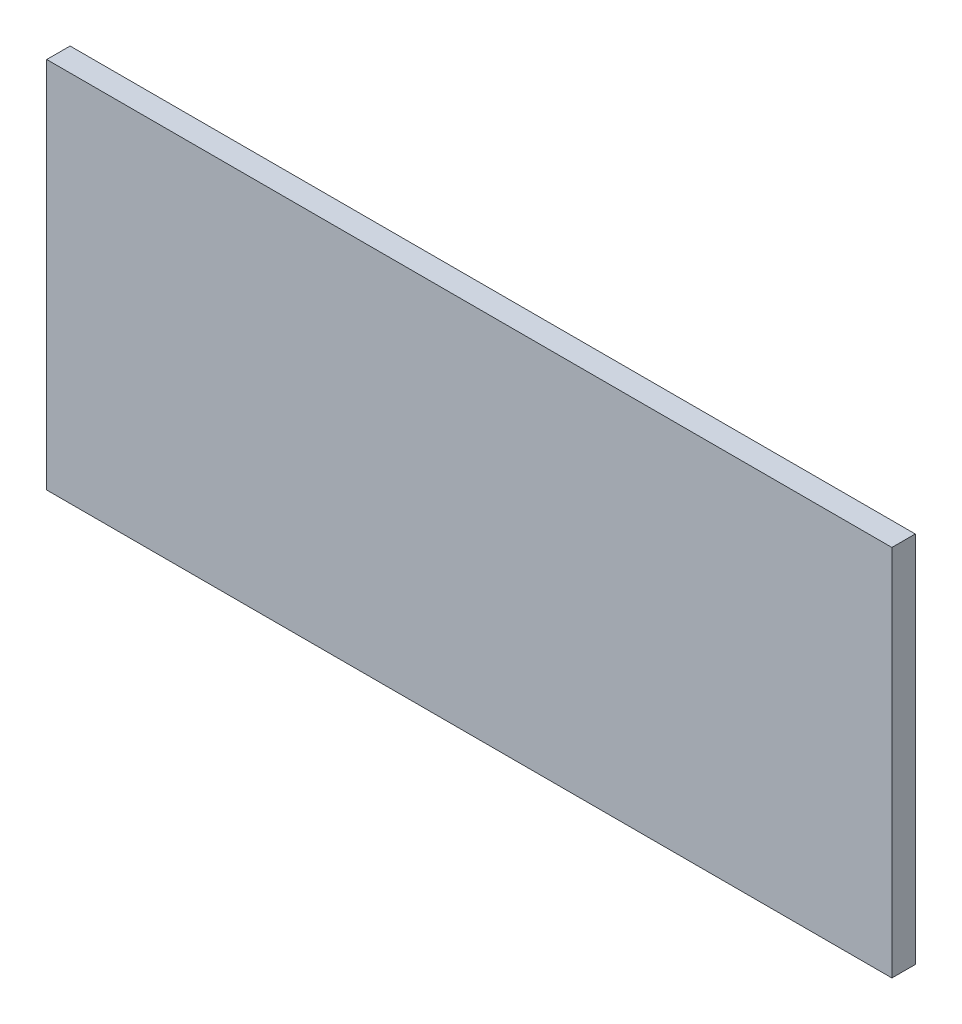
SolidWorks part; units mm, degrees
ref_plane "Front Plane" through (0, 0, 0) normal (0, 0, 1) x (1, 0, 0)
ref_plane "Top Plane" through (0, 0, 0) normal (0, 1, 0) x (1, 0, 0)
ref_plane "Right Plane" through (0, 0, 0) normal (1, 0, 0) x (0, 0, -1)
sketch "Sketch1" plane through (0, 0, 0) normal (0, 0, 1) x (1, 0, 0)
  line L1 (-215.9, -95.25) -> (215.9, -95.25)
  line L2 (-215.9, -95.25) -> (-215.9, 95.25)
  line L3 (-215.9, 95.25) -> (215.9, 95.25)
  line L4 (215.9, -95.25) -> (215.9, 95.25)
  line L5 (-215.9, -95.25) -> (215.9, 95.25) construction
  line L6 (-215.9, 95.25) -> (215.9, -95.25) construction
  point P0 (0, 0)
  dimension "D1" = 431.8
  dimension "D2" = 190.5
extrude "Boss-Extrude1" add sketch "Sketch1" along normal blind 11.938
